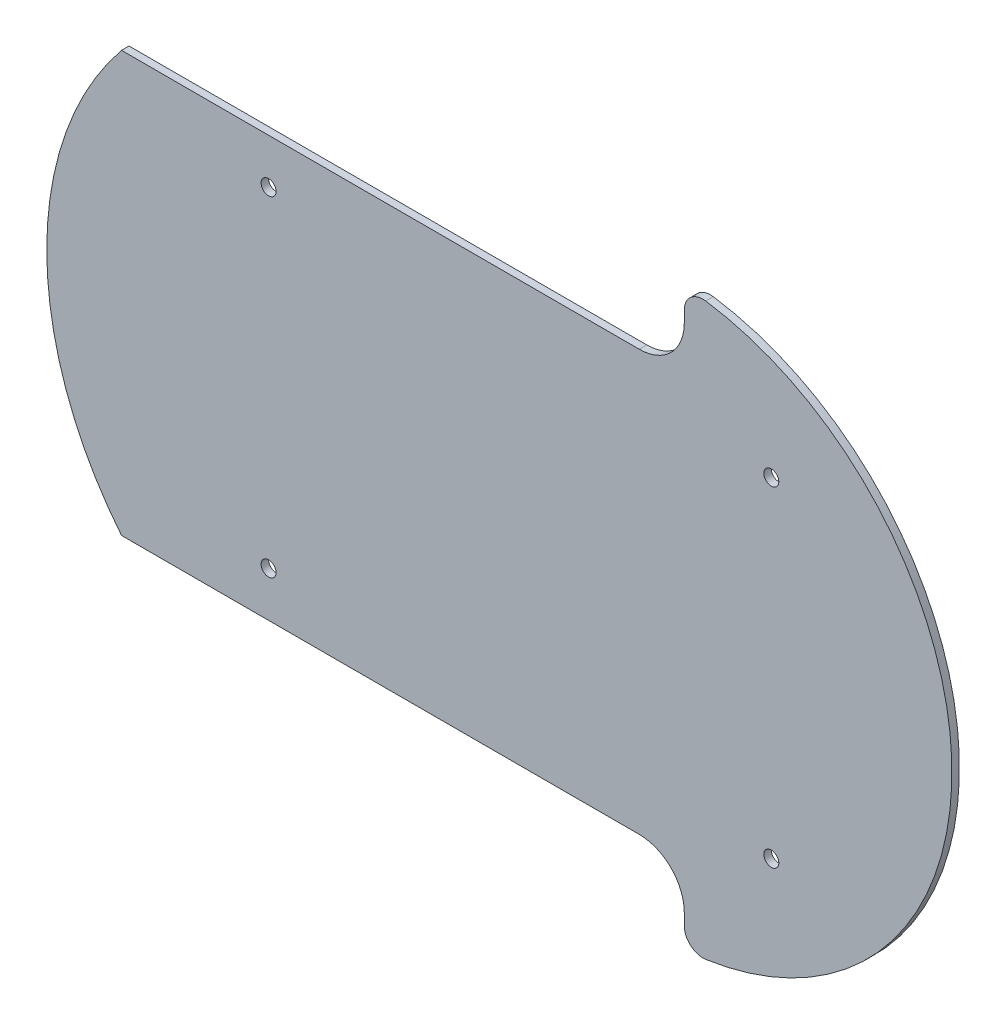
SolidWorks part; units mm, degrees
ref_plane "Front Plane" through (0, 0, 0) normal (0, 0, 1) x (1, 0, 0)
ref_plane "Top Plane" through (0, 0, 0) normal (0, 1, 0) x (1, 0, 0)
ref_plane "Right Plane" through (0, 0, 0) normal (1, 0, 0) x (0, 0, -1)
sketch "Sketch1" plane through (0, 0, 0) normal (0, 0, 1) x (1, 0, 0)
  line L0 (43.801, 68) -> (43.801, 71.0534)
  line L1 (-67, -44) -> (67, -44) construction
  line L2 (-67, -44) -> (-67, 44) construction
  line L3 (-67, 44) -> (67, 44) construction
  line L4 (67, -44) -> (67, 44) construction
  line L5 (-67, -44) -> (67, 44) construction
  line L6 (-67, 44) -> (67, -44) construction
  line L7 (-106.199, -56) -> (31.801, -56)
  line L9 (-106.199, 56) -> (31.801, 56)
  line L11 (-109.5471, -51.6214) -> (67, 31.5721) construction
  line L12 (-109.5471, 51.6214) -> (67, -31.5721) construction
  line L13 (43.801, -68) -> (43.801, -71.0534)
  circle A0 centre (67, 44) radius 2
  circle A1 centre (67, -44) radius 2
  circle A2 centre (-67, 44) radius 2
  circle A3 centre (-67, -44) radius 2
  arc A4 (49.5295, 76) -> (49.5295, -76) centre (38.3374, 0) cw
  arc A5 (43.801, 71.0534) -> (49.5295, 76) centre (48.801, 71.0534) cw
  arc A6 (43.801, -71.0534) -> (49.5295, -76) centre (48.801, -71.0534) ccw
  arc A7 (31.801, 56) -> (43.801, 68) centre (31.801, 68) ccw
  arc A8 (43.801, -68) -> (31.801, -56) centre (31.801, -68) ccw
  arc A9 (-106.199, -56) -> (-106.199, 56) centre (-37.5, 0) cw
  point P0 (0, 0)
  point P15 (0, 0)
  point P16 (0, 0)
  point P17 (0, 0)
  point P19 (0, 0)
  point P26 (0, 0)
  point P27 (0, 0)
  point P30 (43.801, 56)
  point P35 (0, 0)
  point P36 (-105.5472, 56)
  point P37 (0, 0)
  point P38 (0, 0)
  dimension "D1" = 134
  dimension "D4" = 4
  dimension "D5" = 5
  dimension "D6" = 5
  dimension "D3" = 12
  dimension "D10" = 12
  dimension "D11" = 37.5
  dimension "D2" = 88
  dimension "D7" = 38.3374
  dimension "D8" = 12
  dimension "D9" = 12
  dimension "D12" = 150
  dimension "D13" = 20
extrude "Boss-Extrude1" add sketch "Sketch1" along normal blind 2
